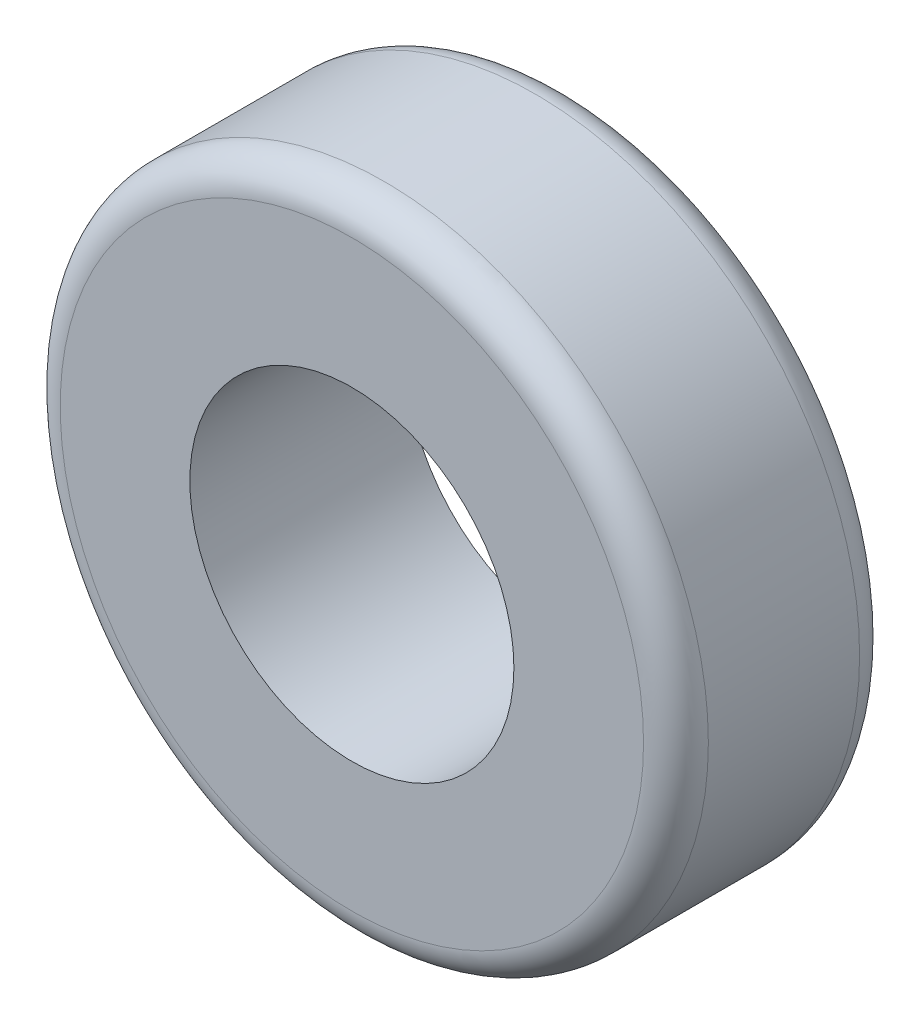
SolidWorks part; units mm, degrees
ref_plane "Front" through (0, 0, 0) normal (0, 0, 1) x (1, 0, 0)
ref_plane "Top" through (0, 0, 0) normal (0, 1, 0) x (1, 0, 0)
ref_plane "Right" through (0, 0, 0) normal (1, 0, 0) x (0, 0, -1)
sketch "Sketch1" plane through (0, 0, 0) normal (0, 0, 1) x (1, 0, 0)
  circle A0 centre (0, 0) radius 15
  circle A1 centre (0, 0) radius 30
extrude "Boss-Extrude1" add sketch "Sketch1" along normal blind 20
fillet "Fillet1" radius 3 2 edges at (30, 0, 0) (30, 0, 20)
